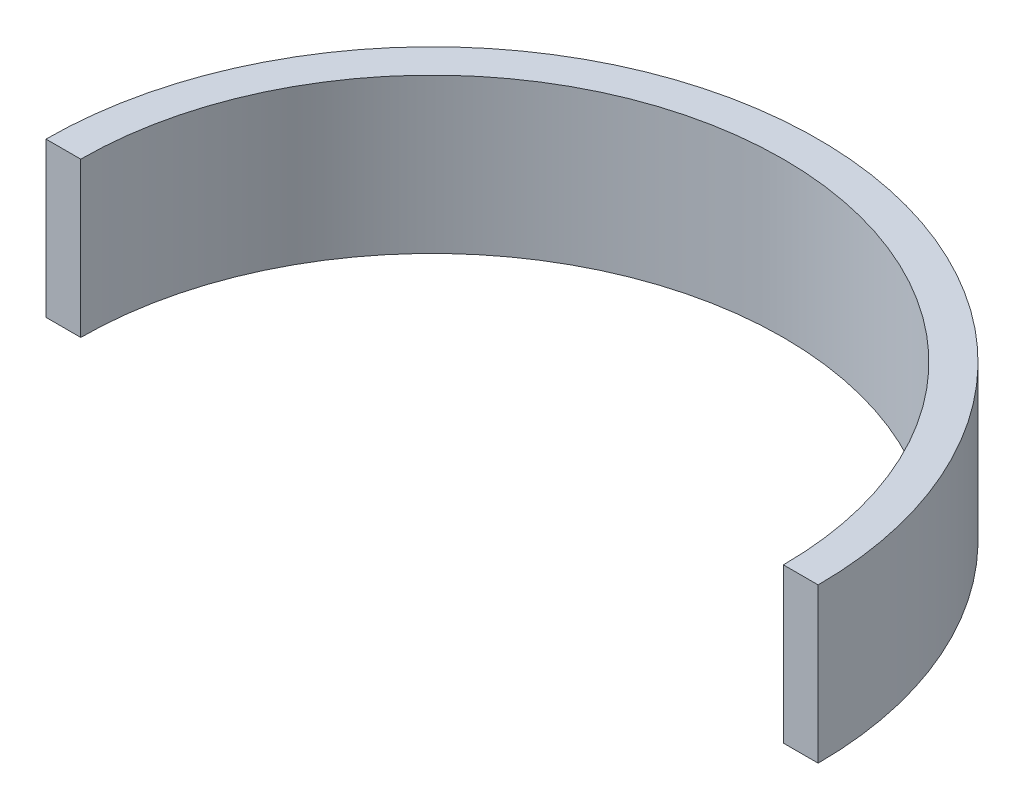
SolidWorks part; units mm, degrees
ref_plane "Front" through (0, 0, 0) normal (0, 0, 1) x (1, 0, 0)
ref_plane "Top" through (0, 0, 0) normal (0, 1, 0) x (1, 0, 0)
ref_plane "Right" through (0, 0, 0) normal (1, 0, 0) x (0, 0, -1)
sketch "草图1" plane through (0, 0, 0) normal (0, 1, 0) x (1, 0, 0)
  line L0 (-46.1099, 0) -> (36.3756, 0) construction
  line L1 (-50, 0) -> (-45.5, 0)
  line L2 (45.5, 0) -> (50, 0)
  arc A0 (-50, 0) -> (50, 0) centre (0, 0) cw
  arc A1 (-45.5, 0) -> (45.5, 0) centre (0, 0) cw
extrude "凸台-拉伸1" add sketch "草图1" along normal blind 20
